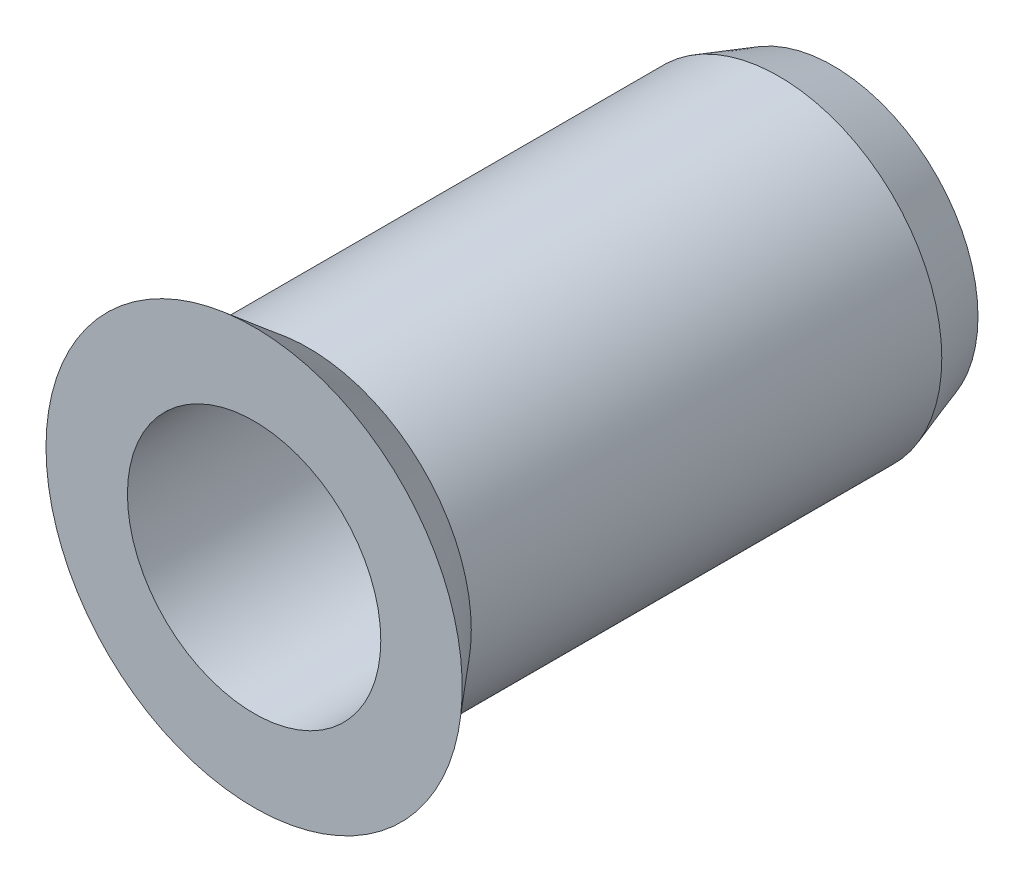
SolidWorks part; units mm, degrees
material "Ст 3 ГОСТ 380-2005"
ref_plane "Спереди" through (0, 0, 0) normal (0, 0, 1) x (1, 0, 0)
ref_plane "Сверху" through (0, 0, 0) normal (0, 1, 0) x (1, 0, 0)
ref_plane "Слева" through (0, 0, 0) normal (1, 0, 0) x (0, 0, -1)
ref_plane "Плоскость1" through (0, 0, 0) normal (0, -1, 0) x (1, 0, 0)
sketch "Эскиз1" plane through (0, 0, 0) normal (0, -1, 0) x (1, 0, 0)
  line L0 (3.5, 9) -> (2.5, 8.3991)
  line L1 (2.5, 8.3991) -> (2.5, 1)
  line L2 (2.5, 1) -> (3.5, 0)
  line L3 (3.5, 0) -> (4, 0)
  line L4 (4, 0) -> (4.5, 1.5)
  line L5 (4.5, 1.5) -> (4.5, 14.5)
  line L6 (4.5, 14.5) -> (5.75, 16)
  line L7 (5.75, 16) -> (3.5, 16)
  line L8 (3.5, 16) -> (3.5, 9)
  line L9 (0, 16) -> (0, 0) construction
  dimension "D1" = 39.806
revolve "Повернуть1" add sketch "Эскиз1" angle 360 about L9
cosmetic thread "Условное изображение резьбы1" parameters "D2"=6
